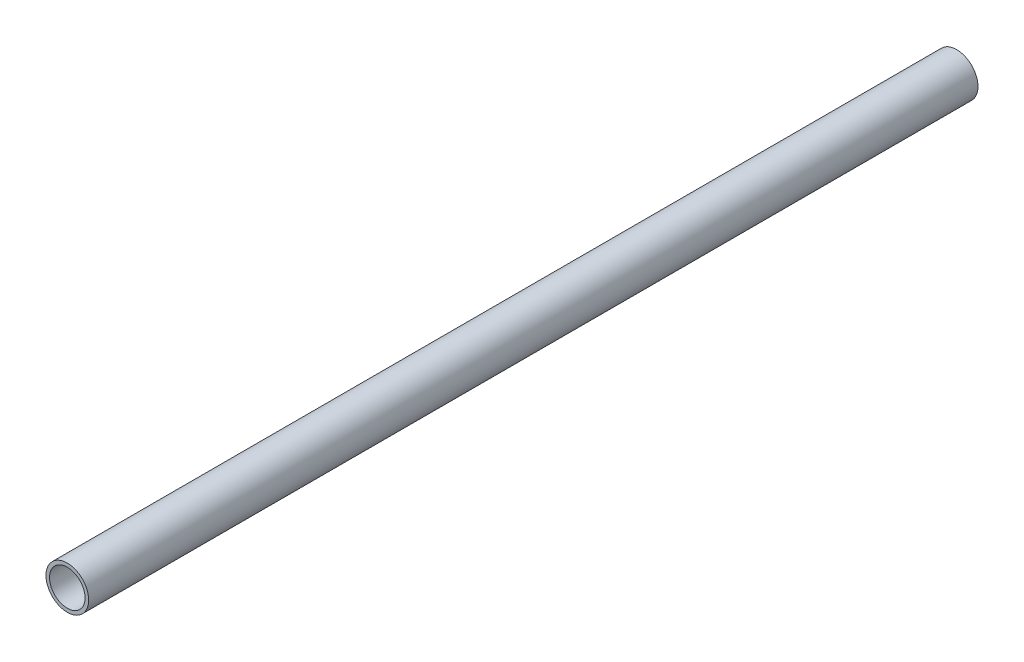
SolidWorks part; units mm, degrees
ref_plane "Plan de face" through (0, 0, 0) normal (0, 0, 1) x (1, 0, 0)
ref_plane "Plan de dessus" through (0, 0, 0) normal (0, 1, 0) x (1, 0, 0)
ref_plane "Plan de droite" through (0, 0, 0) normal (1, 0, 0) x (0, 0, -1)
sketch "Esquisse1" plane through (0, 0, 0) normal (0, 0, 1) x (1, 0, 0)
  circle A0 centre (0, 0) radius 5
  circle A1 centre (0, 0) radius 6
  dimension "D1" = 12
  dimension "D2" = 10
extrude "Boss.-Extru.1" add sketch "Esquisse1" along normal blind 250
